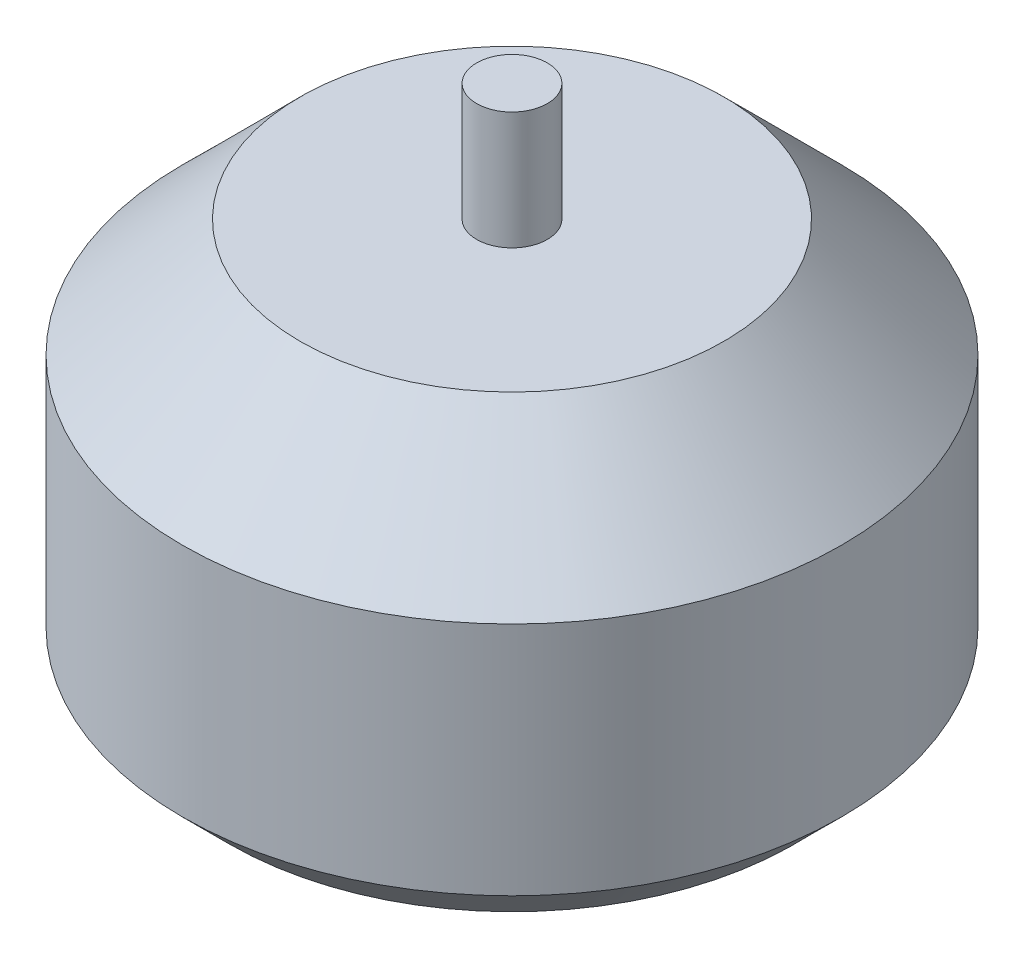
SolidWorks part; units mm, degrees
ref_plane "Front Plane" through (0, 0, 0) normal (0, 0, 1) x (1, 0, 0)
ref_plane "Top Plane" through (0, 0, 0) normal (0, 1, 0) x (1, 0, 0)
ref_plane "Right Plane" through (0, 0, 0) normal (1, 0, 0) x (0, 0, -1)
sketch "Sketch1" plane through (0, 0, 0) normal (0, 1, 0) x (1, 0, 0)
  circle A0 centre (0, 0) radius 14
extrude "Boss-Extrude1" add sketch "Sketch1" along normal blind 17
chamfer "Chamfer1" distance 5 angle 45 1 edges at (0, 17, 14)
chamfer "Chamfer3" distance 2 angle 45 1 edges at (0, 0, 14)
sketch "Sketch3" plane through (0, 0, 0) normal (0, -1, 0) x (1, 0, 0)
  circle A0 centre (0, 9.5) radius 1.65
  circle A1 centre (0, -9.5) radius 1.65
  circle A2 centre (-8, 0) radius 1.65
  circle A3 centre (8, 0) radius 1.65
  dimension "D1" = 9.5
  dimension "D3" = 8
  dimension "D2" = 9.5
  dimension "D4" = 8
extrude "Cut-Extrude1" cut sketch "Sketch3" against normal blind 5
sketch "Sketch4" plane through (0, 17, 0) normal (0, 1, 0) x (1, 0, 0)
  circle A0 centre (0, 0) radius 1.5
extrude "Boss-Extrude2" add sketch "Sketch4" along normal blind 5
